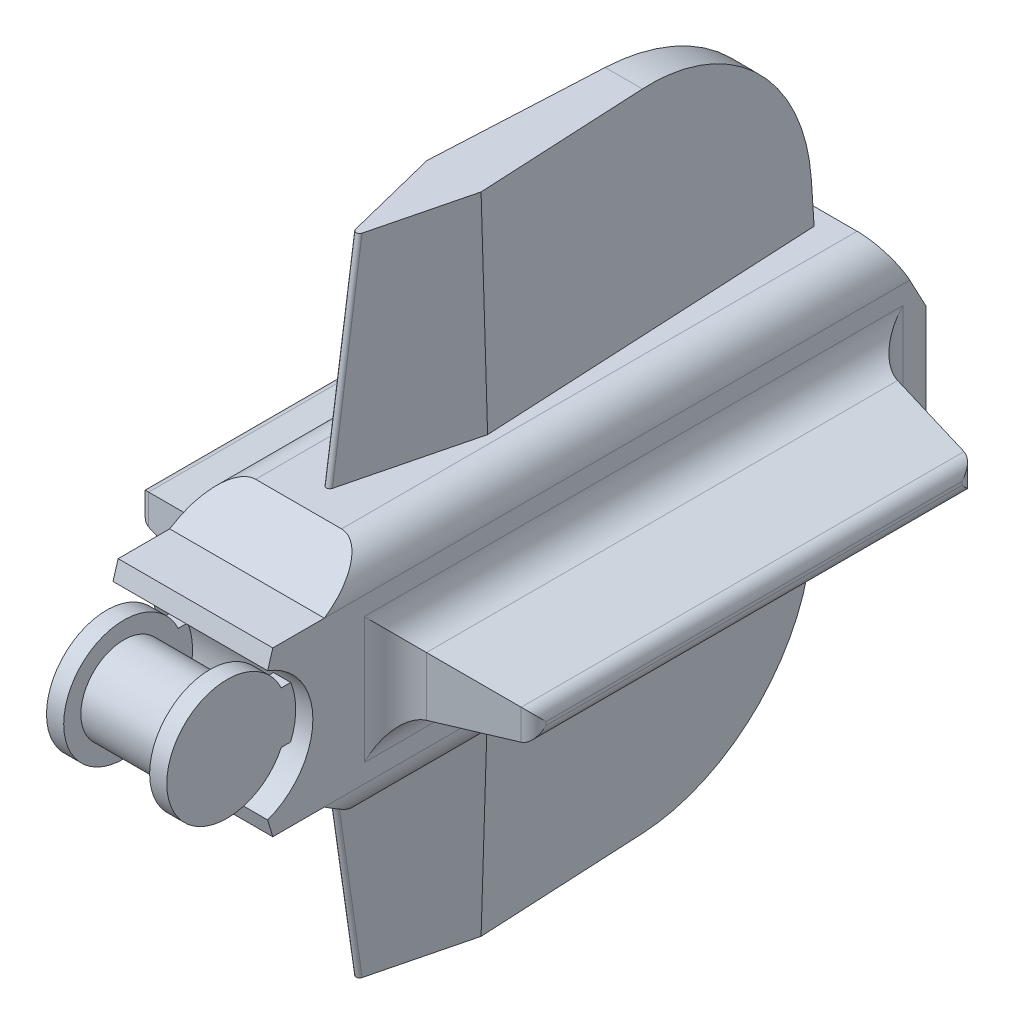
SolidWorks part; units mm, degrees
ref_plane "Front Plane" through (0, 0, 0) normal (0, 0, 1) x (1, 0, 0)
ref_plane "Top Plane" through (0, 0, 0) normal (0, 1, 0) x (1, 0, 0)
ref_plane "Right Plane" through (0, 0, 0) normal (1, 0, 0) x (0, 0, -1)
sketch "Sketch1" plane through (0, 0, 0) normal (1, 0, 0) x (0, 0, -1)
  circle A0 centre (0, 0) radius 3.175
  dimension "D1" = 6.35
extrude "Boss-Extrude1" add sketch "Sketch1" along normal mid plane 6.35
sketch "Sketch2" plane through (3.175, 0, 0) normal (1, 0, 0) x (0, 0, -1)
  circle A0 centre (0, 0) radius 4.445
  dimension "D1" = 8.89
extrude "Boss-Extrude2" add sketch "Sketch2" along normal blind 1.27
mirror "Mirror1" about plane through (0, 0, 0) normal (1, 0, 0) of "Boss-Extrude2"
sketch "Sketch3" plane through (4.445, 0, 0) normal (1, 0, 0) x (0, 0, -1)
  line L1 (0, 1.905) -> (6.35, 1.905)
  line L2 (0, 1.905) -> (0, -1.905)
  line L3 (0, -1.905) -> (6.35, -1.905)
  line L4 (6.35, 1.905) -> (6.35, -1.905)
  point P4 (0, 0)
  dimension "D1" = 3.81
  dimension "D2" = 6.35
extrude "Boss-Extrude3" add sketch "Sketch3" against normal blind 1.27
mirror "Mirror2" about plane through (0, 0, 0) normal (1, 0, 0) of "Boss-Extrude3"
sketch "Sketch4" plane through (-3.175, 0, 0) normal (1, 0, 0) x (0, 0, -1)
  line L0 (1.7375, 4.7736) -> (0, 0) construction
  line L1 (0, 0) -> (5.08, 0) construction
  line L2 (1.7375, 4.7736) -> (2.1185, 6.0436)
  line L3 (2.1185, 6.0436) -> (5.9285, 6.0436)
  line L4 (0, 0) -> (1.7375, -4.7736) construction
  line L5 (5.9285, 6.0436) -> (9.7385, 8.5836)
  line L6 (9.7385, 8.5836) -> (47.8385, 8.5836)
  line L7 (47.8385, 8.5836) -> (50.3785, 3.81)
  line L8 (50.3785, 3.81) -> (50.3785, -3.81)
  line L9 (50.3785, 0) -> (5.08, 0) construction
  line L10 (47.8385, -8.5836) -> (50.3785, -3.81)
  line L11 (9.7385, -8.5836) -> (47.8385, -8.5836)
  line L12 (5.9285, -6.0436) -> (9.7385, -8.5836)
  line L13 (2.1185, -6.0436) -> (5.9285, -6.0436)
  line L14 (1.7375, -4.7736) -> (2.1185, -6.0436)
  arc A0 (1.7375, 4.7736) -> (1.7375, -4.7736) centre (0, 0) cw
  dimension "D1" = 5.08
  dimension "D2" = 140
  dimension "D3" = 1.27
  dimension "D4" = 0.381
  dimension "D5" = 3.81
  dimension "D6" = 3.81
  dimension "D7" = 2.54
  dimension "D8" = 38.1
  dimension "D9" = 7.62
  dimension "D10" = 2.54
extrude "Boss-Extrude4" add sketch "Sketch4" against normal blind 2.54 and the other way blind 8.89
sketch "Sketch5" plane through (0, 0, -50.3785) normal (0, 0, -1) x (-1, 0, 0)
  circle A0 centre (0, 0) radius 3.175
  dimension "D1" = 6.35
extrude "Cut-Extrude1" cut sketch "Sketch5" against normal blind 12.7
fillet "Fillet1" radius 2.54 4 edges at (5.715, -8.5836, -28.7885) (-5.715, -8.5836, -28.7885) (-5.715, 8.5836, -28.7885) (5.715, 8.5836, -28.7885)
sketch "Sketch6" plane through (5.715, 0, 0) normal (1, 0, 0) x (0, 0, -1)
  line L0 (50.3785, -3.81) -> (50.3785, 3.81) construction
  line L1 (11.0085, 2.54) -> (46.5685, 2.54)
  line L2 (11.0085, 2.54) -> (11.0085, -2.54)
  line L3 (11.0085, -2.54) -> (46.5685, -2.54)
  line L4 (46.5685, 2.54) -> (46.5685, -2.54)
  point P4 (11.0085, 0)
  point P6 (50.3785, 0)
  dimension "D1" = 3.81
  dimension "D2" = 5.08
  dimension "D3" = 35.56
extrude "Boss-Extrude5" add sketch "Sketch6" along normal blind 8.89 draft 10
mirror "Mirror3" about plane through (0, 0, 0) normal (1, 0, 0) of "Boss-Extrude5"
fillet "Fillet2" radius 1.016 8 edges at (-14.605, -0.9725, -28.7885) (-14.605, 0, -45.0009) (-14.605, 0.9725, -28.7885) (-14.605, 0, -12.576) (14.605, 0.9725, -28.7885) (14.605, 0, -45.0009) (14.605, -0.9725, -28.7885) (14.605, 0, -12.576)
fillet "Fillet3" radius 2.54 8 edges at (5.715, -2.54, -28.7885) (5.715, 0, -11.0085) (5.715, 0, -46.5685) (5.715, 2.54, -28.7885) (-5.715, 0, -11.0085) (-5.715, 0, -46.5685) (-5.715, -2.54, -28.7885) (-5.715, 2.54, -28.7885)
sketch "Sketch7" plane through (0, 8.5836, 0) normal (0, 1, 0) x (1, 0, 0)
  line L0 (0, 9.7385) -> (0, 47.8385) construction
  line L1 (3.175, 9.7385) -> (-3.175, 9.7385) construction
  line L2 (3.175, 47.8385) -> (-3.175, 47.8385) construction
  line L3 (-1.27, 46.5685) -> (1.27, 46.5685)
  line L4 (1.27, 46.5685) -> (2.54, 21.1685)
  line L5 (2.54, 21.1685) -> (0, 11.0085)
  line L6 (0, 11.0085) -> (-2.54, 21.1685)
  line L7 (-2.54, 21.1685) -> (-1.27, 46.5685)
  point P8 (0, 46.5685)
  dimension "D1" = 2.54
  dimension "D2" = 1.27
  dimension "D3" = 1.27
  dimension "D4" = 2.54
  dimension "D5" = 25.4
extrude "Boss-Extrude6" add sketch "Sketch7" along normal blind 15.24 draft 2
mirror "Mirror4" about plane through (0, 0, 0) normal (0, 1, 0) of "Boss-Extrude6"
fillet "Fillet4" radius 0.254 2 edges at (0, -16.2036, -12.1056) (0, 16.2036, -12.1056)
fillet "Fillet5" radius 12.7 2 edges at (0, -23.8236, -46.0363) (0, 23.8236, -46.0363)
